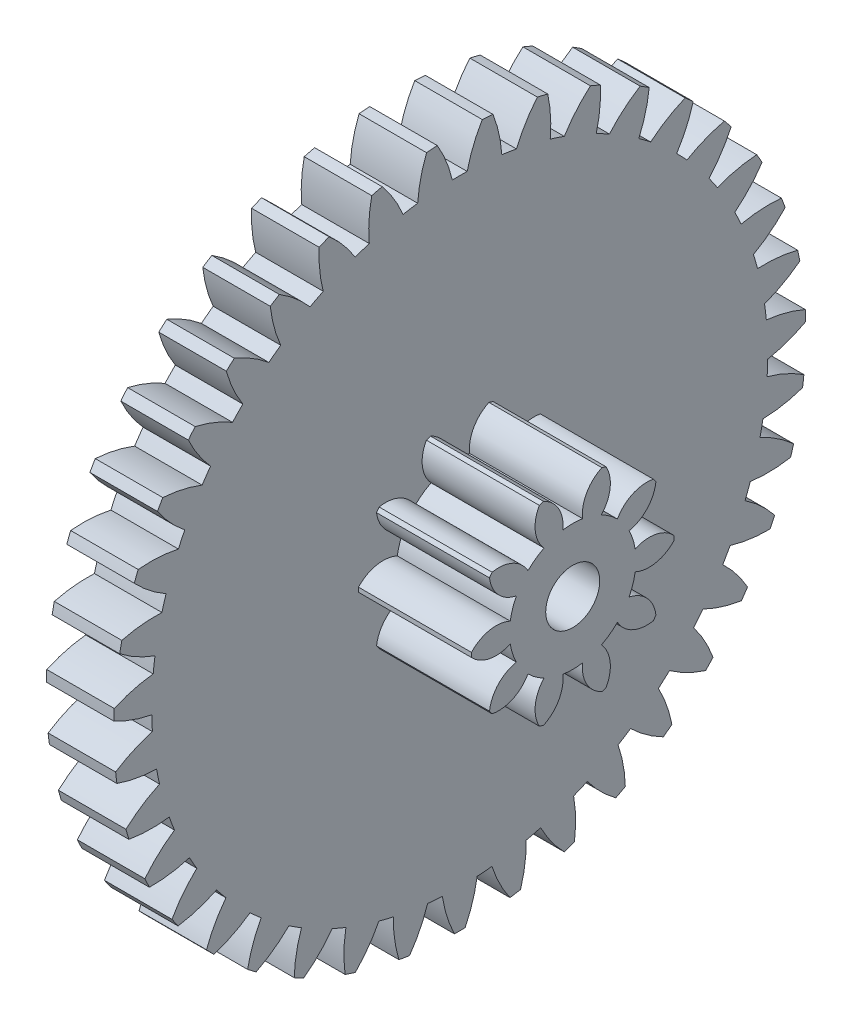
SolidWorks part; units mm, degrees
ref_plane "Plan de face" through (0, 0, 0) normal (0, 0, 1) x (1, 0, 0)
ref_plane "Plan de dessus" through (0, 0, 0) normal (0, 1, 0) x (1, 0, 0)
ref_plane "Plan de droite" through (0, 0, 0) normal (1, 0, 0) x (0, 0, -1)
ref_plane "Plan1" through (0, 0, 0) normal (0, 0, -1) x (-1, 0, 0)
sketch "Esquisse1" plane through (0, 0, 0) normal (0, 0, -1) x (-1, 0, 0)
  line L0 (-1, 5.125) -> (-1, 0)
  line L1 (-1, 0) -> (0, 0)
  line L2 (0, 0) -> (0, 5.125)
  line L3 (0, 5.125) -> (-1, 5.125)
  line L4 (-1, 0) -> (0, 0) construction
revolve "Révolution1" add sketch "Esquisse1" angle 360 about L4
sketch "Esquisse2" plane through (0, 0, 0) normal (-1, 0, 0) x (0, 0, 1)
  arc A0 (-0.4916, 5.1014) -> (-1.1491, 4.9945) centre (0, 0) ccw
  arc A1 (-1.1491, 4.9945) -> (-0.84, 4.4835) centre (-2.6433, 3.7415) cw
  arc A2 (-0.84, 4.4835) -> (-0.623, 4.5187) centre (0, 0) cw
  arc A3 (-0.623, 4.5187) -> (-0.4916, 5.1014) centre (1.3224, 4.386) cw
extrude "Enlèv. mat.-Extru.1" cut sketch "Esquisse2" against normal through all
sketch "Esquisse3" plane through (0, 0, 0) normal (-1, 0, 0) x (0, 0, 1)
  arc A0 (0.3331, 5.1142) -> (-0.3331, 5.1142) centre (0, 0) ccw
  arc A1 (-0.3331, 5.1142) -> (-0.1099, 4.5602) centre (-2.0089, 4.117) cw
  arc A2 (-0.1099, 4.5602) -> (0.1099, 4.5602) centre (0, 0) cw
  arc A3 (0.1099, 4.5602) -> (0.3331, 5.1142) centre (2.0089, 4.117) cw
extrude "Enlèv. mat.-Extru.2" cut sketch "Esquisse3" against normal through all
sketch "Esquisse4" plane through (0, 0, 0) normal (-1, 0, 0) x (0, 0, 1)
  arc A0 (1.1491, 4.9945) -> (0.4916, 5.1014) centre (0, 0) ccw
  arc A1 (0.4916, 5.1014) -> (0.623, 4.5187) centre (-1.3224, 4.386) cw
  arc A2 (0.623, 4.5187) -> (0.84, 4.4835) centre (0, 0) cw
  arc A3 (0.84, 4.4835) -> (1.1491, 4.9945) centre (2.6433, 3.7415) cw
extrude "Enlèv. mat.-Extru.3" cut sketch "Esquisse4" against normal through all
sketch "Esquisse5" plane through (0, 0, 0) normal (-1, 0, 0) x (0, 0, 1)
  arc A0 (1.9354, 4.7455) -> (1.3036, 4.9564) centre (0, 0) ccw
  arc A1 (1.3036, 4.9564) -> (1.3398, 4.3603) centre (-0.6017, 4.5413) cw
  arc A2 (1.3398, 4.3603) -> (1.5483, 4.2907) centre (0, 0) cw
  arc A3 (1.5483, 4.2907) -> (1.9354, 4.7455) centre (3.2092, 3.269) cw
extrude "Enlèv. mat.-Extru.4" cut sketch "Esquisse5" against normal through all
sketch "Esquisse6" plane through (0, 0, 0) normal (-1, 0, 0) x (0, 0, 1)
  arc A0 (2.6716, 4.3736) -> (2.0817, 4.6832) centre (0, 0) ccw
  arc A1 (2.0817, 4.6832) -> (2.0219, 4.0889) centre (0.1345, 4.579) cw
  arc A2 (2.0219, 4.0889) -> (2.2165, 3.9868) centre (0, 0) cw
  arc A3 (2.2165, 3.9868) -> (2.6716, 4.3736) centre (3.692, 2.7119) cw
extrude "Enlèv. mat.-Extru.5" cut sketch "Esquisse6" against normal through all
sketch "Esquisse7" plane through (0, 0, 0) normal (-1, 0, 0) x (0, 0, 1)
  arc A0 (3.3386, 3.8884) -> (2.806, 4.2886) centre (0, 0) ccw
  arc A1 (2.806, 4.2886) -> (2.6516, 3.7116) centre (0.8673, 4.4981) cw
  arc A2 (2.6516, 3.7116) -> (2.8273, 3.5796) centre (0, 0) cw
  arc A3 (2.8273, 3.5796) -> (3.3386, 3.8884) centre (4.0793, 2.0845) cw
extrude "Enlèv. mat.-Extru.6" cut sketch "Esquisse7" against normal through all
sketch "Esquisse8" plane through (0, 0, 0) normal (-1, 0, 0) x (0, 0, 1)
  arc A0 (3.9191, 3.3025) -> (3.4576, 3.7829) centre (0, 0) ccw
  arc A1 (3.4576, 3.7829) -> (3.2127, 3.2382) centre (1.5776, 4.3008) cw
  arc A2 (3.2127, 3.2382) -> (3.3649, 3.0797) centre (0, 0) cw
  arc A3 (3.3649, 3.0797) -> (3.9191, 3.3025) centre (4.3608, 1.4032) cw
extrude "Enlèv. mat.-Extru.7" cut sketch "Esquisse8" against normal through all
sketch "Esquisse9" plane through (0, 0, 0) normal (-1, 0, 0) x (0, 0, 1)
  arc A0 (4.3981, 2.6311) -> (4.0197, 3.1793) centre (0, 0) ccw
  arc A1 (4.0197, 3.1793) -> (3.6905, 2.6809) centre (2.2471, 3.992) cw
  arc A2 (3.6905, 2.6809) -> (3.8154, 2.5) centre (0, 0) cw
  arc A3 (3.8154, 2.5) -> (4.3981, 2.6311) centre (4.5294, 0.6855) cw
extrude "Enlèv. mat.-Extru.8" cut sketch "Esquisse9" against normal through all
sketch "Esquisse10" plane through (0, 0, 0) normal (-1, 0, 0) x (0, 0, 1)
  arc A0 (4.7632, 1.8915) -> (4.4776, 2.4933) centre (0, 0) ccw
  arc A1 (4.4776, 2.4933) -> (4.0728, 2.0542) centre (2.8584, 3.5799) cw
  arc A2 (4.0728, 2.0542) -> (4.167, 1.8556) centre (0, 0) cw
  arc A3 (4.167, 1.8556) -> (4.7632, 1.8915) centre (4.5807, -0.05) cw
extrude "Enlèv. mat.-Extru.9" cut sketch "Esquisse10" against normal through all
sketch "Esquisse11" plane through (0, 0, 0) normal (-1, 0, 0) x (0, 0, 1)
  arc A0 (5.0049, 1.1029) -> (4.8196, 1.7428) centre (0, 0) ccw
  arc A1 (4.8196, 1.7428) -> (4.3496, 1.3743) centre (3.3956, 3.075) cw
  arc A2 (4.3496, 1.3743) -> (4.4107, 1.1632) centre (0, 0) cw
  arc A3 (4.4107, 1.1632) -> (5.0049, 1.1029) centre (4.5134, -0.7841) cw
extrude "Enlèv. mat.-Extru.10" cut sketch "Esquisse11" against normal through all
sketch "Esquisse12" plane through (0, 0, 0) normal (-1, 0, 0) x (0, 0, 1)
  arc A0 (5.117, 0.2858) -> (5.0367, 0.9471) centre (0, 0) ccw
  arc A1 (5.0367, 0.9471) -> (4.5137, 0.6588) centre (3.8449, 2.4905) cw
  arc A2 (4.5137, 0.6588) -> (4.5402, 0.4406) centre (0, 0) cw
  arc A3 (4.5402, 0.4406) -> (5.117, 0.2858) centre (4.3292, -1.498) cw
extrude "Enlèv. mat.-Extru.11" cut sketch "Esquisse12" against normal through all
sketch "Esquisse13" plane through (0, 0, 0) normal (-1, 0, 0) x (0, 0, 1)
  arc A0 (5.0966, -0.5387) -> (5.1234, 0.1269) centre (0, 0) ccw
  arc A1 (5.1234, 0.1269) -> (4.5609, -0.0738) centre (4.1946, 1.8415) cw
  arc A2 (4.5609, -0.0738) -> (4.5521, -0.2934) centre (0, 0) cw
  arc A3 (4.5521, -0.2934) -> (5.0966, -0.5387) centre (4.0328, -2.173) cw
extrude "Enlèv. mat.-Extru.12" cut sketch "Esquisse13" against normal through all
sketch "Esquisse14" plane through (0, 0, 0) normal (-1, 0, 0) x (0, 0, 1)
  arc A0 (4.9442, -1.3493) -> (5.0774, -0.6966) centre (0, 0) ccw
  arc A1 (5.0774, -0.6966) -> (4.49, -0.8045) centre (4.4357, 1.1448) cw
  arc A2 (4.49, -0.8045) -> (4.446, -1.0198) centre (0, 0) cw
  arc A3 (4.446, -1.0198) -> (4.9442, -1.3493) centre (3.632, -2.7918) cw
extrude "Enlèv. mat.-Extru.13" cut sketch "Esquisse14" against normal through all
sketch "Esquisse15" plane through (0, 0, 0) normal (-1, 0, 0) x (0, 0, 1)
  arc A0 (4.6637, -2.1249) -> (4.8999, -1.5021) centre (0, 0) ccw
  arc A1 (4.8999, -1.5021) -> (4.3028, -1.5143) centre (4.5619, 0.4184) cw
  arc A2 (4.3028, -1.5143) -> (4.2249, -1.7198) centre (0, 0) cw
  arc A3 (4.2249, -1.7198) -> (4.6637, -2.1249) centre (3.1371, -3.3382) cw
extrude "Enlèv. mat.-Extru.14" cut sketch "Esquisse15" against normal through all
sketch "Esquisse16" plane through (0, 0, 0) normal (-1, 0, 0) x (0, 0, 1)
  arc A0 (4.2625, -2.8455) -> (4.5955, -2.2686) centre (0, 0) ccw
  arc A1 (4.5955, -2.2686) -> (4.0042, -2.1849) centre (4.5699, -0.3188) cw
  arc A2 (4.0042, -2.1849) -> (3.8943, -2.3753) centre (0, 0) cw
  arc A3 (3.8943, -2.3753) -> (4.2625, -2.8455) centre (2.561, -3.7982) cw
extrude "Enlèv. mat.-Extru.15" cut sketch "Esquisse16" against normal through all
sketch "Esquisse17" plane through (0, 0, 0) normal (-1, 0, 0) x (0, 0, 1)
  arc A0 (3.7508, -3.4924) -> (4.1721, -2.9764) centre (0, 0) ccw
  arc A1 (4.1721, -2.9764) -> (3.6018, -2.7989) centre (4.4596, -1.0477) cw
  arc A2 (3.6018, -2.7989) -> (3.4628, -2.9692) centre (0, 0) cw
  arc A3 (3.4628, -2.9692) -> (3.7508, -3.4924) centre (1.9186, -4.1599) cw
extrude "Enlèv. mat.-Extru.16" cut sketch "Esquisse17" against normal through all
sketch "Esquisse18" plane through (0, 0, 0) normal (-1, 0, 0) x (0, 0, 1)
  arc A0 (3.142, -4.0489) -> (3.6406, -3.6071) centre (0, 0) ccw
  arc A1 (3.6406, -3.6071) -> (3.1062, -3.3405) centre (4.2338, -1.7495) cw
  arc A2 (3.1062, -3.3405) -> (2.9417, -3.4862) centre (0, 0) cw
  arc A3 (2.9417, -3.4862) -> (3.142, -4.0489) centre (1.2264, -4.4138) cw
extrude "Enlèv. mat.-Extru.17" cut sketch "Esquisse18" against normal through all
sketch "Esquisse19" plane through (0, 0, 0) normal (-1, 0, 0) x (0, 0, 1)
  arc A0 (2.4518, -4.5005) -> (3.0149, -4.1444) centre (0, 0) ccw
  arc A1 (3.0149, -4.1444) -> (2.5301, -3.7955) centre (3.8983, -2.406) cw
  arc A2 (2.5301, -3.7955) -> (2.3444, -3.9129) centre (0, 0) cw
  arc A3 (2.3444, -3.9129) -> (2.4518, -4.5005) centre (0.5025, -4.5534) cw
extrude "Enlèv. mat.-Extru.18" cut sketch "Esquisse19" against normal through all
sketch "Esquisse20" plane through (0, 0, 0) normal (-1, 0, 0) x (0, 0, 1)
  arc A0 (1.6982, -4.8355) -> (2.311, -4.5744) centre (0, 0) ccw
  arc A1 (2.311, -4.5744) -> (1.8885, -4.1522) centre (3.4619, -3.0002) cw
  arc A2 (1.8885, -4.1522) -> (1.6863, -4.2383) centre (0, 0) cw
  arc A3 (1.6863, -4.2383) -> (1.6982, -4.8355) centre (-0.2344, -4.575) cw
extrude "Enlèv. mat.-Extru.19" cut sketch "Esquisse20" against normal through all
sketch "Esquisse21" plane through (0, 0, 0) normal (-1, 0, 0) x (0, 0, 1)
  arc A0 (0.9005, -5.0453) -> (1.5473, -4.8858) centre (0, 0) ccw
  arc A1 (1.5473, -4.8858) -> (1.198, -4.4014) centre (2.9358, -3.5167) cw
  arc A2 (1.198, -4.4014) -> (0.9846, -4.454) centre (0, 0) cw
  arc A3 (0.9846, -4.454) -> (0.9005, -5.0453) centre (-0.9652, -4.4782) cw
extrude "Enlèv. mat.-Extru.20" cut sketch "Esquisse21" against normal through all
sketch "Esquisse22" plane through (0, 0, 0) normal (-1, 0, 0) x (0, 0, 1)
  arc A0 (0.0795, -5.1244) -> (0.7435, -5.0708) centre (0, 0) ccw
  arc A1 (0.7435, -5.0708) -> (0.4765, -4.5365) centre (2.3336, -3.942) cw
  arc A2 (0.4765, -4.5365) -> (0.2574, -4.5542) centre (0, 0) cw
  arc A3 (0.2574, -4.5542) -> (0.0795, -5.1244) centre (-1.6711, -4.2653) cw
extrude "Enlèv. mat.-Extru.21" cut sketch "Esquisse22" against normal through all
sketch "Esquisse23" plane through (0, 0, 0) normal (-1, 0, 0) x (0, 0, 1)
  arc A0 (-0.7435, -5.0708) -> (-0.0795, -5.1244) centre (0, 0) ccw
  arc A1 (-0.0795, -5.1244) -> (-0.2574, -4.5542) centre (1.6711, -4.2653) cw
  arc A2 (-0.2574, -4.5542) -> (-0.4765, -4.5365) centre (0, 0) cw
  arc A3 (-0.4765, -4.5365) -> (-0.7435, -5.0708) centre (-2.3336, -3.942) cw
extrude "Enlèv. mat.-Extru.22" cut sketch "Esquisse23" against normal through all
sketch "Esquisse24" plane through (0, 0, 0) normal (-1, 0, 0) x (0, 0, 1)
  arc A0 (-1.5473, -4.8858) -> (-0.9005, -5.0453) centre (0, 0) ccw
  arc A1 (-0.9005, -5.0453) -> (-0.9846, -4.454) centre (0.9652, -4.4782) cw
  arc A2 (-0.9846, -4.454) -> (-1.198, -4.4014) centre (0, 0) cw
  arc A3 (-1.198, -4.4014) -> (-1.5473, -4.8858) centre (-2.9358, -3.5167) cw
extrude "Enlèv. mat.-Extru.23" cut sketch "Esquisse24" against normal through all
sketch "Esquisse25" plane through (0, 0, 0) normal (-1, 0, 0) x (0, 0, 1)
  arc A0 (-2.311, -4.5744) -> (-1.6982, -4.8355) centre (0, 0) ccw
  arc A1 (-1.6982, -4.8355) -> (-1.6863, -4.2383) centre (0.2344, -4.575) cw
  arc A2 (-1.6863, -4.2383) -> (-1.8885, -4.1522) centre (0, 0) cw
  arc A3 (-1.8885, -4.1522) -> (-2.311, -4.5744) centre (-3.4619, -3.0002) cw
extrude "Enlèv. mat.-Extru.24" cut sketch "Esquisse25" against normal through all
sketch "Esquisse26" plane through (0, 0, 0) normal (-1, 0, 0) x (0, 0, 1)
  arc A0 (-3.0149, -4.1444) -> (-2.4518, -4.5005) centre (0, 0) ccw
  arc A1 (-2.4518, -4.5005) -> (-2.3444, -3.9129) centre (-0.5025, -4.5534) cw
  arc A2 (-2.3444, -3.9129) -> (-2.5301, -3.7955) centre (0, 0) cw
  arc A3 (-2.5301, -3.7955) -> (-3.0149, -4.1444) centre (-3.8983, -2.406) cw
extrude "Enlèv. mat.-Extru.25" cut sketch "Esquisse26" against normal through all
sketch "Esquisse27" plane through (0, 0, 0) normal (-1, 0, 0) x (0, 0, 1)
  arc A0 (-3.6406, -3.6071) -> (-3.142, -4.0489) centre (0, 0) ccw
  arc A1 (-3.142, -4.0489) -> (-2.9417, -3.4862) centre (-1.2264, -4.4138) cw
  arc A2 (-2.9417, -3.4862) -> (-3.1062, -3.3405) centre (0, 0) cw
  arc A3 (-3.1062, -3.3405) -> (-3.6406, -3.6071) centre (-4.2338, -1.7495) cw
extrude "Enlèv. mat.-Extru.26" cut sketch "Esquisse27" against normal through all
sketch "Esquisse28" plane through (0, 0, 0) normal (-1, 0, 0) x (0, 0, 1)
  arc A0 (-4.1721, -2.9764) -> (-3.7508, -3.4924) centre (0, 0) ccw
  arc A1 (-3.7508, -3.4924) -> (-3.4628, -2.9692) centre (-1.9186, -4.1599) cw
  arc A2 (-3.4628, -2.9692) -> (-3.6018, -2.7989) centre (0, 0) cw
  arc A3 (-3.6018, -2.7989) -> (-4.1721, -2.9764) centre (-4.4596, -1.0477) cw
extrude "Enlèv. mat.-Extru.27" cut sketch "Esquisse28" against normal through all
sketch "Esquisse29" plane through (0, 0, 0) normal (-1, 0, 0) x (0, 0, 1)
  arc A0 (-4.5955, -2.2686) -> (-4.2625, -2.8455) centre (0, 0) ccw
  arc A1 (-4.2625, -2.8455) -> (-3.8943, -2.3753) centre (-2.561, -3.7982) cw
  arc A2 (-3.8943, -2.3753) -> (-4.0042, -2.1849) centre (0, 0) cw
  arc A3 (-4.0042, -2.1849) -> (-4.5955, -2.2686) centre (-4.5699, -0.3188) cw
extrude "Enlèv. mat.-Extru.28" cut sketch "Esquisse29" against normal through all
sketch "Esquisse30" plane through (0, 0, 0) normal (-1, 0, 0) x (0, 0, 1)
  arc A0 (-4.8999, -1.5021) -> (-4.6637, -2.1249) centre (0, 0) ccw
  arc A1 (-4.6637, -2.1249) -> (-4.2249, -1.7198) centre (-3.1371, -3.3382) cw
  arc A2 (-4.2249, -1.7198) -> (-4.3028, -1.5143) centre (0, 0) cw
  arc A3 (-4.3028, -1.5143) -> (-4.8999, -1.5021) centre (-4.5619, 0.4184) cw
extrude "Enlèv. mat.-Extru.29" cut sketch "Esquisse30" against normal through all
sketch "Esquisse31" plane through (0, 0, 0) normal (-1, 0, 0) x (0, 0, 1)
  arc A0 (-5.0774, -0.6966) -> (-4.9442, -1.3493) centre (0, 0) ccw
  arc A1 (-4.9442, -1.3493) -> (-4.446, -1.0198) centre (-3.632, -2.7918) cw
  arc A2 (-4.446, -1.0198) -> (-4.49, -0.8045) centre (0, 0) cw
  arc A3 (-4.49, -0.8045) -> (-5.0774, -0.6966) centre (-4.4357, 1.1448) cw
extrude "Enlèv. mat.-Extru.30" cut sketch "Esquisse31" against normal through all
sketch "Esquisse32" plane through (0, 0, 0) normal (-1, 0, 0) x (0, 0, 1)
  arc A0 (-5.1234, 0.1269) -> (-5.0966, -0.5387) centre (0, 0) ccw
  arc A1 (-5.0966, -0.5387) -> (-4.5521, -0.2934) centre (-4.0328, -2.173) cw
  arc A2 (-4.5521, -0.2934) -> (-4.5609, -0.0738) centre (0, 0) cw
  arc A3 (-4.5609, -0.0738) -> (-5.1234, 0.1269) centre (-4.1946, 1.8415) cw
extrude "Enlèv. mat.-Extru.31" cut sketch "Esquisse32" against normal through all
sketch "Esquisse33" plane through (0, 0, 0) normal (-1, 0, 0) x (0, 0, 1)
  arc A0 (-5.0367, 0.9471) -> (-5.117, 0.2858) centre (0, 0) ccw
  arc A1 (-5.117, 0.2858) -> (-4.5402, 0.4406) centre (-4.3292, -1.498) cw
  arc A2 (-4.5402, 0.4406) -> (-4.5137, 0.6588) centre (0, 0) cw
  arc A3 (-4.5137, 0.6588) -> (-5.0367, 0.9471) centre (-3.8449, 2.4905) cw
extrude "Enlèv. mat.-Extru.32" cut sketch "Esquisse33" against normal through all
sketch "Esquisse34" plane through (0, 0, 0) normal (-1, 0, 0) x (0, 0, 1)
  arc A0 (-4.8196, 1.7428) -> (-5.0049, 1.1029) centre (0, 0) ccw
  arc A1 (-5.0049, 1.1029) -> (-4.4107, 1.1632) centre (-4.5134, -0.7841) cw
  arc A2 (-4.4107, 1.1632) -> (-4.3496, 1.3743) centre (0, 0) cw
  arc A3 (-4.3496, 1.3743) -> (-4.8196, 1.7428) centre (-3.3956, 3.075) cw
extrude "Enlèv. mat.-Extru.33" cut sketch "Esquisse34" against normal through all
sketch "Esquisse35" plane through (0, 0, 0) normal (-1, 0, 0) x (0, 0, 1)
  arc A0 (-4.4776, 2.4933) -> (-4.7632, 1.8915) centre (0, 0) ccw
  arc A1 (-4.7632, 1.8915) -> (-4.167, 1.8556) centre (-4.5807, -0.05) cw
  arc A2 (-4.167, 1.8556) -> (-4.0728, 2.0542) centre (0, 0) cw
  arc A3 (-4.0728, 2.0542) -> (-4.4776, 2.4933) centre (-2.8584, 3.5799) cw
extrude "Enlèv. mat.-Extru.34" cut sketch "Esquisse35" against normal through all
sketch "Esquisse36" plane through (0, 0, 0) normal (-1, 0, 0) x (0, 0, 1)
  arc A0 (-4.0197, 3.1793) -> (-4.3981, 2.6311) centre (0, 0) ccw
  arc A1 (-4.3981, 2.6311) -> (-3.8154, 2.5) centre (-4.5294, 0.6855) cw
  arc A2 (-3.8154, 2.5) -> (-3.6905, 2.6809) centre (0, 0) cw
  arc A3 (-3.6905, 2.6809) -> (-4.0197, 3.1793) centre (-2.2471, 3.992) cw
extrude "Enlèv. mat.-Extru.35" cut sketch "Esquisse36" against normal through all
sketch "Esquisse37" plane through (0, 0, 0) normal (-1, 0, 0) x (0, 0, 1)
  arc A0 (-3.4576, 3.7829) -> (-3.9191, 3.3025) centre (0, 0) ccw
  arc A1 (-3.9191, 3.3025) -> (-3.3649, 3.0797) centre (-4.3608, 1.4032) cw
  arc A2 (-3.3649, 3.0797) -> (-3.2127, 3.2382) centre (0, 0) cw
  arc A3 (-3.2127, 3.2382) -> (-3.4576, 3.7829) centre (-1.5776, 4.3008) cw
extrude "Enlèv. mat.-Extru.36" cut sketch "Esquisse37" against normal through all
sketch "Esquisse38" plane through (0, 0, 0) normal (-1, 0, 0) x (0, 0, 1)
  arc A0 (-2.806, 4.2886) -> (-3.3386, 3.8884) centre (0, 0) ccw
  arc A1 (-3.3386, 3.8884) -> (-2.8273, 3.5796) centre (-4.0793, 2.0845) cw
  arc A2 (-2.8273, 3.5796) -> (-2.6516, 3.7116) centre (0, 0) cw
  arc A3 (-2.6516, 3.7116) -> (-2.806, 4.2886) centre (-0.8673, 4.4981) cw
extrude "Enlèv. mat.-Extru.37" cut sketch "Esquisse38" against normal through all
sketch "Esquisse39" plane through (0, 0, 0) normal (-1, 0, 0) x (0, 0, 1)
  arc A0 (-2.0817, 4.6832) -> (-2.6716, 4.3736) centre (0, 0) ccw
  arc A1 (-2.6716, 4.3736) -> (-2.2165, 3.9868) centre (-3.692, 2.7119) cw
  arc A2 (-2.2165, 3.9868) -> (-2.0219, 4.0889) centre (0, 0) cw
  arc A3 (-2.0219, 4.0889) -> (-2.0817, 4.6832) centre (-0.1345, 4.579) cw
extrude "Enlèv. mat.-Extru.38" cut sketch "Esquisse39" against normal through all
sketch "Esquisse40" plane through (0, 0, 0) normal (-1, 0, 0) x (0, 0, 1)
  arc A0 (-1.3036, 4.9564) -> (-1.9354, 4.7455) centre (0, 0) ccw
  arc A1 (-1.9354, 4.7455) -> (-1.5483, 4.2907) centre (-3.2092, 3.269) cw
  arc A2 (-1.5483, 4.2907) -> (-1.3398, 4.3603) centre (0, 0) cw
  arc A3 (-1.3398, 4.3603) -> (-1.3036, 4.9564) centre (0.6017, 4.5413) cw
extrude "Enlèv. mat.-Extru.39" cut sketch "Esquisse40" against normal through all
sketch "Esquisse41" plane through (1, 0, 0) normal (1, 0, 0) x (0, 0, -1)
  arc A0 (0.6621, 0.6623) -> (1.1939, 0.9081) centre (1.098, 0.4174) cw
  arc A1 (1.1939, 0.9081) -> (1.2326, 0.8548) centre (0, 0) cw
  arc A2 (1.2326, 0.8548) -> (0.8345, 0.425) centre (0.7362, 0.9152) cw
  arc A3 (0.8345, 0.425) -> (0.9249, 0.1467) centre (0, 0) cw
  arc A4 (0.9249, 0.1467) -> (1.4996, 0.0329) centre (1.1336, -0.3077) cw
  arc A5 (1.4996, 0.0329) -> (1.4996, -0.0329) centre (0, 0) cw
  arc A6 (1.4996, -0.0329) -> (0.9249, -0.1467) centre (1.1336, 0.3077) cw
  arc A7 (0.9249, -0.1467) -> (0.8345, -0.425) centre (0, 0) cw
  arc A8 (0.8345, -0.425) -> (1.2326, -0.8548) centre (0.7362, -0.9152) cw
  arc A9 (1.2326, -0.8548) -> (1.1939, -0.9081) centre (0, 0) cw
  arc A10 (1.1939, -0.9081) -> (0.6621, -0.6623) centre (1.098, -0.4174) cw
  arc A11 (0.6621, -0.6623) -> (0.4253, -0.8343) centre (0, 0) cw
  arc A12 (0.4253, -0.8343) -> (0.4947, -1.4161) centre (0.0577, -1.1732) cw
  arc A13 (0.4947, -1.4161) -> (0.4321, -1.4364) centre (0, 0) cw
  arc A14 (0.4321, -1.4364) -> (0.1463, -0.925) centre (0.6429, -0.983) cw
  arc A15 (0.1463, -0.925) -> (-0.1463, -0.925) centre (0, 0) cw
  arc A16 (-0.1463, -0.925) -> (-0.4321, -1.4364) centre (-0.6429, -0.983) cw
  arc A17 (-0.4321, -1.4364) -> (-0.4947, -1.4161) centre (0, 0) cw
  arc A18 (-0.4947, -1.4161) -> (-0.4253, -0.8343) centre (-0.0577, -1.1732) cw
  arc A19 (-0.4253, -0.8343) -> (-0.6621, -0.6623) centre (0, 0) cw
  arc A20 (-0.6621, -0.6623) -> (-1.1939, -0.9081) centre (-1.098, -0.4174) cw
  arc A21 (-1.1939, -0.9081) -> (-1.2326, -0.8548) centre (0, 0) cw
  arc A22 (-1.2326, -0.8548) -> (-0.8345, -0.425) centre (-0.7362, -0.9152) cw
  arc A23 (-0.8345, -0.425) -> (-0.9249, -0.1467) centre (0, 0) cw
  arc A24 (-0.9249, -0.1467) -> (-1.4996, -0.0329) centre (-1.1336, 0.3077) cw
  arc A25 (-1.4996, -0.0329) -> (-1.4996, 0.0329) centre (0, 0) cw
  arc A26 (-1.4996, 0.0329) -> (-0.9249, 0.1467) centre (-1.1336, -0.3077) cw
  arc A27 (-0.9249, 0.1467) -> (-0.8345, 0.425) centre (0, 0) cw
  arc A28 (-0.8345, 0.425) -> (-1.2326, 0.8548) centre (-0.7362, 0.9152) cw
  arc A29 (-1.2326, 0.8548) -> (-1.1939, 0.9081) centre (0, 0) cw
  arc A30 (-1.1939, 0.9081) -> (-0.6621, 0.6623) centre (-1.098, 0.4174) cw
  arc A31 (-0.6621, 0.6623) -> (-0.4253, 0.8343) centre (0, 0) cw
  arc A32 (-0.4253, 0.8343) -> (-0.4947, 1.4161) centre (-0.0577, 1.1732) cw
  arc A33 (-0.4947, 1.4161) -> (-0.4321, 1.4364) centre (0, 0) cw
  arc A34 (-0.4321, 1.4364) -> (-0.1463, 0.925) centre (-0.6429, 0.983) cw
  arc A35 (-0.1463, 0.925) -> (0.1463, 0.925) centre (0, 0) cw
  arc A36 (0.1463, 0.925) -> (0.4321, 1.4364) centre (0.6429, 0.983) cw
  arc A37 (0.4321, 1.4364) -> (0.4947, 1.4161) centre (0, 0) cw
  arc A38 (0.4947, 1.4161) -> (0.4253, 0.8343) centre (0.0577, 1.1732) cw
  arc A39 (0.4253, 0.8343) -> (0.6621, 0.6623) centre (0, 0) cw
extrude "Boss.-Extru.1" add sketch "Esquisse41" along normal blind 1.6728
hole_wizard "Diamètre du perçage Ø0.8 (0.8)1" positions "Esquisse43" profile "Esquisse42" hole size "Ø0.8" standard "Ansi Metric"
sketch "Esquisse43" plane through (0, 0, 0) normal (-1, 0, 0) x (0, 0, 1)
  point P0 (0, 0)
sketch "Esquisse42" plane through (0, 0, 0) normal (0, 1, 0) x (0, 0, 1)
  line L0 (0, 0) -> (0, 2.6728)
  line L1 (0, 2.6728) -> (0.4, 2.6728)
  line L2 (0.4, 2.6728) -> (0.4, 0)
  line L5 (0.4, 0) -> (0, 0)
  line L11 (0, -6.35) -> (0, 107.95) construction
  dimension "Diamètre du perçage jusqu'au prochain" = 0.8
  dimension "Profondeur du perçage jusqu'au prochain" = 2.6728
